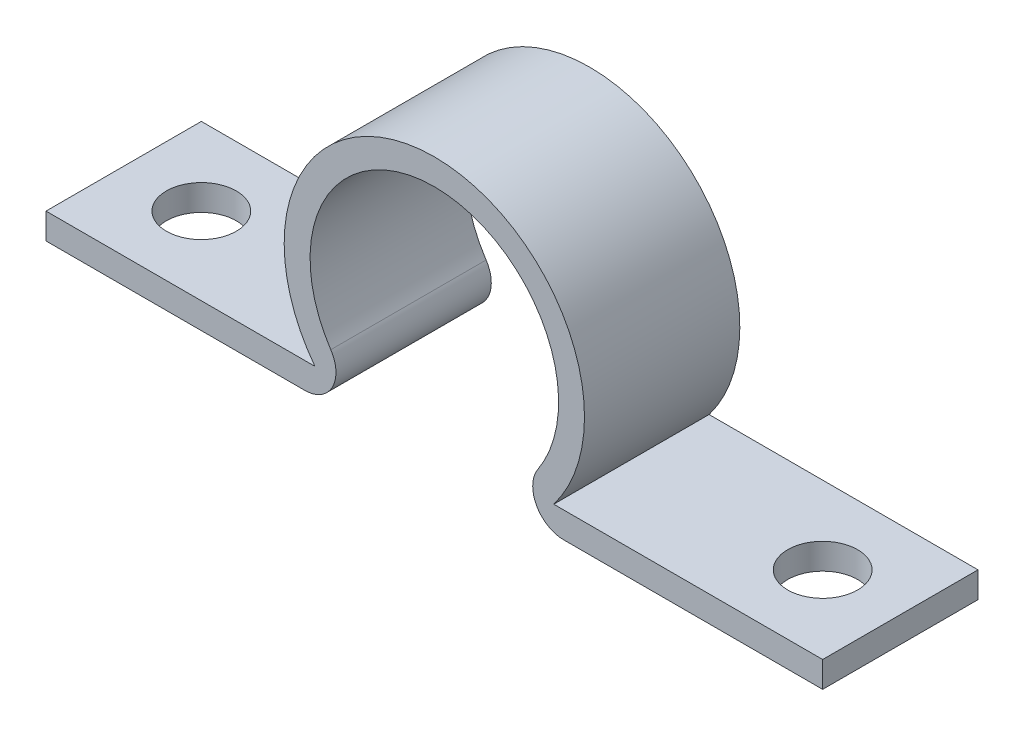
SolidWorks part; units mm, degrees
ref_plane "Front Plane" through (0, 0, 0) normal (0, 0, 1) x (1, 0, 0)
ref_plane "Top Plane" through (0, 0, 0) normal (0, 1, 0) x (1, 0, 0)
ref_plane "Right Plane" through (0, 0, 0) normal (1, 0, 0) x (0, 0, -1)
sketch "Sketch1" plane through (0, 0, 0) normal (0, 0, 1) x (1, 0, 0)
  line L0 (0, 0) -> (50, 0)
  line L1 (100, 0) -> (150, 0)
  line L2 (0, 5) -> (5, 5)
  line L3 (5, 5) -> (51.9385, 5)
  line L4 (0, 5) -> (0, 0)
  line L5 (150, 5) -> (150, 0)
  line L6 (83.1242, 0) -> (150, 0) construction
  line L7 (98.0615, 5) -> (150, 5)
  line L8 (5, 5) -> (5, 5) construction
  line L9 (0, 0) -> (66.8758, 0) construction
  arc A0 (55, 9.3166) -> (95, 9.3166) centre (75, 22.5831) cw
  arc A1 (51.9385, 5) -> (98.0615, 5) centre (75, 22.5831) cw
  arc A2 (66.8758, 0) -> (83.1242, 0) centre (75, 22.5831) cw construction
  arc A3 (95, 9.3166) -> (100, 0) centre (100, 6) ccw
  arc A4 (50, 0) -> (55, 9.3166) centre (50, 6) ccw
  dimension "D1" = 24
  dimension "D4" = 6
  dimension "D2" = 150
  dimension "D5" = 50
  dimension "D3" = 5
extrude "Boss-Extrude1" add sketch "Sketch1" along normal blind 30
hole_wizard "M12 Clearance Hole2" positions "Sketch4" profile "Sketch5" hole size "M12" standard "IS" end condition through all
sketch "Sketch4" plane through (0, 5, 0) normal (0, 1, 0) x (1, 0, 0)
  line L0 (150, -30) -> (150, 0) construction
  line L1 (0, -30) -> (0, 0) construction
  point P0 (15, -15)
  point P2 (135, -15)
  dimension "D1" = 15
  dimension "D2" = 15
sketch "Sketch5" plane through (15, 5, 15) normal (1, 0, 0) x (0, 0, 1)
  line L0 (0, 0) -> (0, 5)
  line L1 (0, 5) -> (6.75, 5)
  line L2 (6.75, 5) -> (6.75, 0)
  line L5 (6.75, 0) -> (0, 0)
  line L11 (0, -6.35) -> (0, 107.95) construction
  dimension "Thru Hole Dia." = 13.5
  dimension "Thru Hole Depth" = 5
